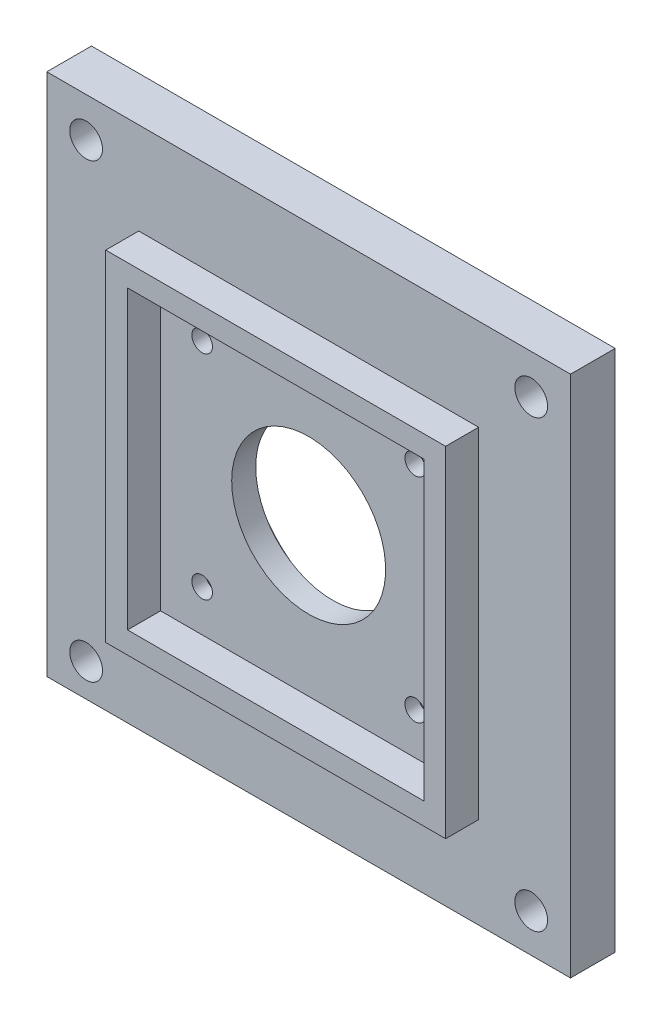
SolidWorks part; units mm, degrees
material "Hexcel AS4C (3000 Filaments)"
ref_plane "Front" through (0, 0, 0) normal (0, 0, 1) x (1, 0, 0)
ref_plane "Top" through (0, 0, 0) normal (0, 1, 0) x (1, 0, 0)
ref_plane "Right" through (0, 0, 0) normal (1, 0, 0) x (0, 0, -1)
sketch "Sketch4" plane through (0, 0, 0) normal (0, 0, 1) x (1, 0, 0)
  line L0 (0, -42.8625) -> (0, 41.275) construction
  line L1 (-49.15, -15.5) -> (-80.15, 15.5) construction
  line L2 (-80.15, -15.5) -> (-49.15, 15.5) construction
  line L3 (-39.925, 44.5615) -> (-39.925, -66.5635) construction
  line L4 (-71.275, 44.5615) -> (-71.275, -66.5635) construction
  line L8 (-62.05, 15.5) -> (-31.05, -15.5) construction
  line L9 (-31.05, 15.5) -> (-62.05, -15.5) construction
  line L11 (-31.05, 36.624) -> (-31.05, -53.8635) construction
  line L12 (43.75, 0) -> (-164.4633, 0) construction
  line L13 (-62.05, 36.624) -> (-62.05, -53.8635) construction
  line L14 (-49.15, 36.624) -> (-49.15, -53.8635) construction
  line L15 (-80.15, 36.624) -> (-80.15, -53.8635) construction
  line L16 (-113.2228, 15.5) -> (-0.2036, 15.5) construction
  line L17 (-113.2228, -15.5) -> (-0.2036, -15.5) construction
  line L18 (-25, -66.5635) -> (-25, 44.5615) construction
  line L19 (-68.1, -66.5635) -> (-68.1, 44.5615) construction
  line L20 (-43.1, 44.5615) -> (-43.1, -66.5635) construction
  line L21 (-86.2, -66.5635) -> (-86.2, 44.5615) construction
  line L22 (5.8397, -21.55) -> (-134.1626, -21.55) construction
  line L23 (5.8397, 21.55) -> (-134.1626, 21.55) construction
  line L24 (10.9249, -24.725) -> (-138.6228, -24.725) construction
  line L25 (10.9249, 24.725) -> (-138.6228, 24.725) construction
  line L26 (-89.375, 44.5615) -> (-89.375, -66.5635) construction
  line L27 (-21.825, 44.5615) -> (-21.825, -66.5635) construction
  circle A0 centre (0, 0) radius 12.7 construction
  circle A1 centre (0, 0) radius 15.875 construction
  circle A2 centre (0, 0) radius 9.46 construction
  circle A3 centre (-93.65, 0) radius 9.46 construction
  arc A4 (-93.65, 12.7) -> (-93.65, -12.7) centre (-93.65, 0) ccw construction
  circle A5 centre (27.27, 0) radius 9.46 construction
  circle A6 centre (27.27, 0) radius 12.7 construction
  circle A7 centre (-120.3675, 0) radius 9.46 construction
  circle A8 centre (-120.3675, 0) radius 12.7 construction
  point P3 (0, 0)
  point P6 (-49.15, -15.5)
  point P11 (-93.65, 0)
  point P12 (-49.15, 15.5)
  point P13 (-46.55, 0)
  point P14 (-80.15, 15.5)
  point P15 (-80.15, -15.5)
  point P61 (-64.65, 0)
  point P65 (27.27, 0)
  point P66 (-120.3675, 0)
  dimension "D20" = 3.175
  dimension "D18" = 29
  dimension "D26" = 73.82
  dimension "D27" = 64.65
  dimension "D2" = 31
  dimension "D3" = 25
  dimension "D4" = 31
  dimension "D5" = 21.825
  dimension "D6" = 15.5
  dimension "D7" = 15.5
  dimension "D8" = 6.05
  dimension "D9" = 6.05
  dimension "D10" = 6.05
  dimension "D11" = 6.05
  dimension "D12" = 6.05
  dimension "D13" = 6.05
  dimension "D14" = 3.175
  dimension "D15" = 3.175
  dimension "D16" = 3.175
  dimension "D17" = 3.175
  dimension "D19" = 3.175
  dimension "D21" = 3.175
  dimension "D22" = 46.55
  dimension "D23" = 47.1
  dimension "D24" = 58.32
  dimension "D25" = 147.6375
sketch "Sketch5" plane through (0, 0, 0) normal (0, 0, 1) x (1, 0, 0)
  line L0 (-25, -21.55) -> (-25, 21.55)
  line L1 (-25, -66.5635) -> (-25, 44.5615) construction
  line L2 (5.8397, -21.55) -> (-134.1626, -21.55) construction
  line L3 (5.8397, 21.55) -> (-134.1626, 21.55) construction
  line L4 (-25, 21.55) -> (-68.1, 21.55)
  line L6 (-68.1, -66.5635) -> (-68.1, 44.5615) construction
  line L7 (-68.1, 21.55) -> (-68.1, -21.55)
  line L8 (-68.1, -21.55) -> (-25, -21.55)
  line L9 (-21.825, 24.725) -> (-21.825, -24.725)
  line L10 (10.9249, 24.725) -> (-138.6228, 24.725) construction
  line L11 (-21.825, 44.5615) -> (-21.825, -66.5635) construction
  line L12 (10.9249, -24.725) -> (-138.6228, -24.725) construction
  line L13 (-21.825, -24.725) -> (-71.275, -24.725)
  line L14 (-71.275, 44.5615) -> (-71.275, -66.5635) construction
  line L15 (-71.275, -24.725) -> (-71.275, 24.725)
  line L16 (-71.275, 24.725) -> (-21.825, 24.725)
extrude "Extrude1" add sketch "Sketch5" along normal blind 4.8
sketch "Sketch6" plane through (0, 0, 0) normal (0, 0, -1) x (-1, 0, 0)
  line L0 (8.45, 83.4705) -> (8.45, -75.5808) construction
  line L1 (84.65, 274.6375) -> (84.65, -282.0493) construction
  line L2 (409.575, -38.1) -> (-293.1783, -38.1) construction
  line L3 (387.35, 38.1) -> (-330.5618, 38.1) construction
  line L4 (8.45, 38.1) -> (8.45, -37.987)
  line L5 (8.45, -37.987) -> (84.65, -38.1)
  line L6 (84.65, -38.1) -> (84.65, 38.1)
  line L7 (84.65, 38.1) -> (8.45, 38.1)
  line L8 (14.17, 92.075) -> (14.17, -77.5708) construction
  line L9 (78.93, 88.9) -> (78.93, -84.1375) construction
  line L10 (-44.45, 32.38) -> (120.65, 32.38) construction
  line L11 (-14.2875, -32.38) -> (123.825, -32.38) construction
  circle A0 centre (62.05, 15.5) radius 1.5
  circle A1 centre (31.05, 15.5) radius 1.5
  circle A2 centre (62.05, -15.5) radius 1.5
  circle A3 centre (31.05, -15.5) radius 1.5
  circle A4 centre (14.17, 32.38) radius 2.3812
  circle A5 centre (78.93, 32.38) radius 2.3813
  circle A6 centre (78.93, -33.3094) radius 2.3813
  circle A7 centre (14.17, -32.38) radius 2.3812
  circle A8 centre (46.55, 0) radius 11.2
  dimension "D1" = 38.1
  dimension "D9" = 64.76
  dimension "D2" = 76.2
  dimension "D3" = 38.1
  dimension "D4" = 76.2
  dimension "D5" = 5.72
  dimension "D6" = 5.72
  dimension "D7" = 5.72
  dimension "D8" = 5.72
extrude "Extrude2" add sketch "Sketch6" along normal blind 6.5
sketch "Sketch7" plane through (0, 0, -6.5) normal (0, 0, -1) x (-1, 0, 0)
  circle A2 centre (62.05, -15.5) radius 6
  circle A3 centre (31.05, -15.5) radius 6
extrude "Extrude3" cut sketch "Sketch7" against normal blind 4.5
sketch "Sketch8" plane through (0, 0, -6.5) normal (0, 0, -1) x (-1, 0, 0)
  circle A0 centre (62.05, 15.5) radius 6
  circle A1 centre (31.05, 15.5) radius 6
extrude "Extrude4" cut sketch "Sketch8" against normal blind 3.5
sketch "Sketch9" plane through (0, 0, -6.5) normal (0, 0, -1) x (-1, 0, 0)
  line L0 (31.05, 15.5) -> (62.05, -15.5) construction
  line L1 (31.05, -15.5) -> (62.05, 15.5) construction
  line L2 (22.225, 10) -> (71.4375, 10) construction
  line L3 (22.225, -10) -> (71.4375, -10) construction
  line L4 (36.55, 23.8125) -> (36.55, -23.8125) construction
  line L5 (56.55, 23.8125) -> (56.55, -25.4) construction
  circle A0 centre (46.55, 0) radius 15.3625
  dimension "D1" = 10
  dimension "D2" = 10
  dimension "D3" = 10
  dimension "D4" = 10
extrude "Extrude5" cut sketch "Sketch9" against normal blind 3
